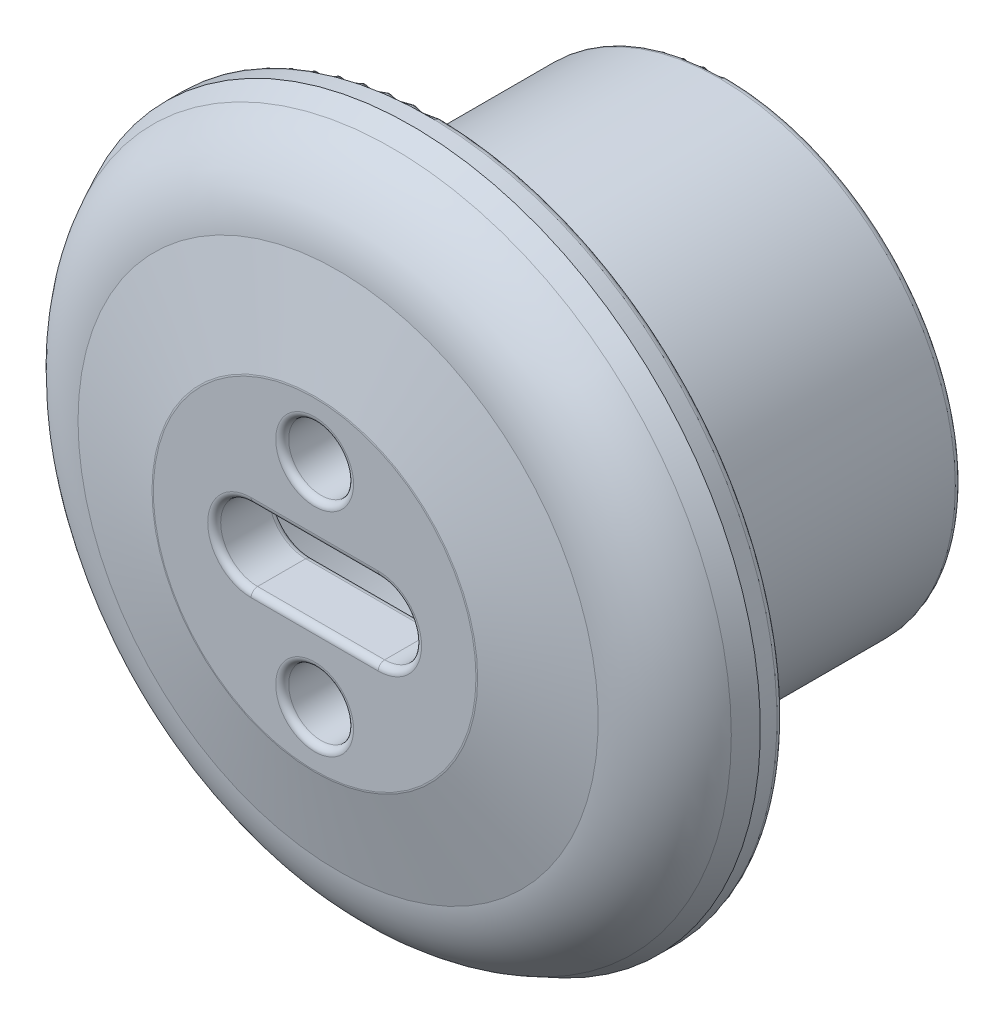
SolidWorks part; units mm, degrees
ref_plane "Front Plane" through (0, 0, 0) normal (0, 0, 1) x (1, 0, 0)
ref_plane "Top Plane" through (0, 0, 0) normal (0, 1, 0) x (1, 0, 0)
ref_plane "Right Plane" through (0, 0, 0) normal (1, 0, 0) x (0, 0, -1)
sketch "Sketch1" plane through (0, 0, 0) normal (1, 0, 0) x (0, 0, -1)
  line L0 (0, 0) -> (0, 10.75) construction
  line L1 (0, 10.75) -> (3, 10.75) construction
  line L3 (2.3972, 10.456) -> (3, 10.75)
  line L4 (3, 10.75) -> (3.7122, 10.75)
  line L5 (3.7122, 10.75) -> (3.7122, 8.75)
  line L6 (3.7122, 8.75) -> (4.7122, 8.75)
  line L7 (4.7122, 8.75) -> (4.7122, 7.25)
  line L8 (4.7122, 7.25) -> (12.7122, 7.25)
  line L11 (0, 0) -> (0, 5)
  line L12 (0, 5) -> (0.7238, 8.0226)
  line L13 (12.7122, 7.25) -> (12.7122, 6.25)
  line L14 (12.7122, 6.25) -> (3.2567, 6.25)
  line L18 (1.8825, 0) -> (0, 0)
  line L19 (3.2567, 6.25) -> (2.8825, 6.25)
  line L20 (1.8825, 5.25) -> (1.8825, 0)
  arc A0 (0.7238, 8.0226) -> (2.3972, 10.456) centre (3.7122, 7.7596) cw
  arc A1 (2.8825, 6.25) -> (1.8825, 5.25) centre (2.8825, 5.25) ccw
  dimension "D3" = 3
  dimension "D10" = 1
  dimension "D1" = 10.75
  dimension "D2" = 3
  dimension "D4" = 2
  dimension "D5" = 1
  dimension "D6" = 1.5
  dimension "D7" = 8
  dimension "D8" = 1
  dimension "D9" = 5
revolve "Revolve1" add sketch "Sketch1" angle 360 about L18
fillet "Fillet2" radius 0.2 4 edges at (-6.25, 0, -12.7122) (-10.75, 0, -3.7122) (-8.75, 0, -4.7122) (-7.25, 0, -12.7122)
sketch "Sketch2" plane through (0, 0, 0) normal (0, 0, 1) x (1, 0, 0)
  line L0 (-1.9596, 0) -> (1.9596, 0) construction
  line L1 (-1.9596, 1.1382) -> (1.9596, 1.1382)
  line L2 (-1.9596, -1.1382) -> (1.9596, -1.1382)
  line L3 (0, 0) -> (0, 3.2744) construction
  line L4 (0, 0) -> (6.2637, 0) construction
  line L5 (6.2637, 0) -> (-6.8437, 0) construction
  arc A0 (-1.9596, 1.1382) -> (-1.9596, -1.1382) centre (-1.9596, 0) ccw
  arc A1 (1.9596, -1.1382) -> (1.9596, 1.1382) centre (1.9596, 0) ccw
  circle A2 centre (0, 3.2744) radius 1
  circle A3 centre (0, -3.2744) radius 1
  point P2 (0, 0)
  dimension "D1" = 2
extrude "Cut-Extrude1" cut sketch "Sketch2" against normal blind 10
fillet "Fillet3" radius 0.2 13 edges at (0, 1.1382, -1.8825) (3.0978, 0, -1.8825) (0, -1.1382, -1.8825) (-3.0978, 0, -1.8825) (-1, 3.2744, -1.8825) (-1, -3.2744, -1.8825) (-5, 0, 0) (0, -1.1382, 0) (3.0978, 0, 0) (0, 1.1382, 0) (-3.0978, 0, 0) (1, 3.2744, 0) (-1, -3.2744, 0)
